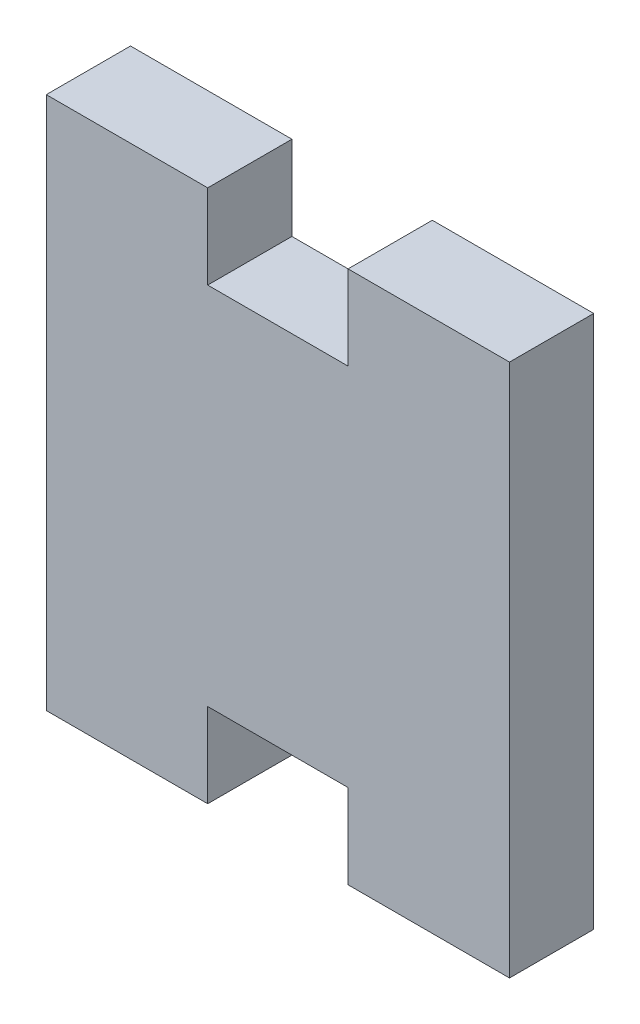
SolidWorks part; units mm, degrees
material "MDF"
ref_plane "Plano frontal" through (0, 0, 0) normal (0, 0, 1) x (1, 0, 0)
ref_plane "Plano superior" through (0, 0, 0) normal (0, 1, 0) x (1, 0, 0)
ref_plane "Plano direito" through (0, 0, 0) normal (1, 0, 0) x (0, 0, -1)
sketch "Esboço1" plane through (0, 0, 0) normal (0, 0, 1) x (1, 0, 0)
  line L0 (-25.5, 0) -> (25.5, 0) construction
  line L1 (-25.5, -19) -> (16.5, -19)
  line L2 (-25.5, -19) -> (-25.5, 19)
  line L3 (-25.5, 19) -> (16.5, 19)
  line L4 (16.5, -19) -> (16.5, 19)
  line L5 (-25.5, -19) -> (16.5, 19) construction
  line L6 (-25.5, 19) -> (16.5, -19) construction
  line L7 (5, 13) -> (-5, 13)
  line L8 (5, 13) -> (5, 19)
  line L9 (5, 19) -> (-5, 19)
  line L10 (-5, 13) -> (-5, 19)
  line L11 (5, 13) -> (-5, 19) construction
  line L12 (5, 19) -> (-5, 13) construction
  line L13 (5, -19) -> (-5, -19)
  line L14 (-5, -13) -> (-5, -19)
  line L15 (5, -13) -> (-5, -13)
  line L16 (5, -13) -> (5, -19)
  line L17 (-25.5, 13) -> (-16.5, 13)
  line L18 (-16.5, 13) -> (-16.5, -13)
  line L19 (-16.5, -13) -> (-25.5, -13)
  line L20 (-25.5, -13) -> (-25.5, 13)
  line L21 (-16.5, -13) -> (-16.5, -19)
  line L22 (-16.5, 13) -> (-16.5, 19)
  line L23 (-16.5, -13) -> (16.5, -13) construction
  point P0 (0, 0)
  point P6 (0, 16)
  point P13 (0, 0)
  point P20 (-16.5, 0)
  point P27 (0, -13)
  point P28 (16.5, 0)
  point P30 (0, 15.0933)
  point P31 (0, 0)
  point P32 (16.9104, -19)
  point P33 (0, 0)
  dimension "D5" = 9
  dimension "D1" = 38
  dimension "D2" = 10
  dimension "D3" = 42
  dimension "D4" = 6
extrude "Ressalto-extrusão1" add sketch "Esboço1" along normal blind 6 contours L15 L16 L1 L4 L3 L8 L7 L10 L2 L14
